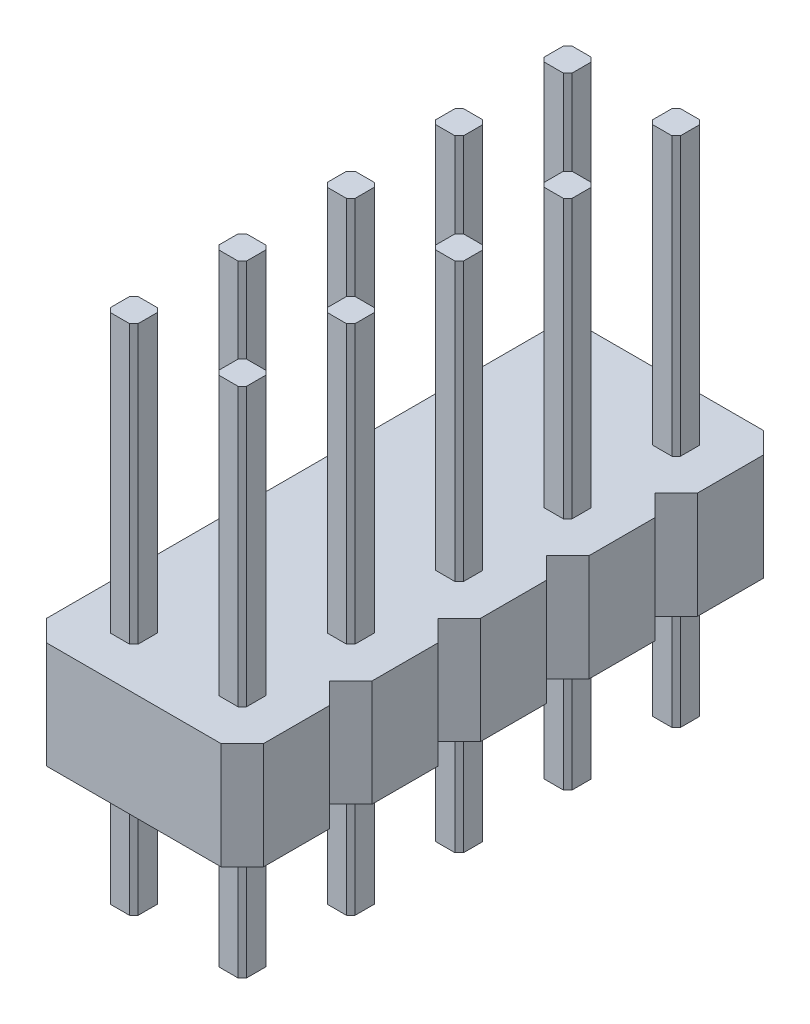
SolidWorks part; units mm, degrees
ref_plane "Front Plane" through (0, 0, 0) normal (0, 0, 1) x (1, 0, 0)
ref_plane "Top Plane" through (0, 0, 0) normal (0, 1, 0) x (1, 0, 0)
ref_plane "Right Plane" through (0, 0, 0) normal (1, 0, 0) x (0, 0, -1)
sketch "Sketch1" plane through (0, 0, 0) normal (0, 1, 0) x (1, 0, 0)
  line L0 (-0.325, 0.225) -> (-0.225, 0.325)
  line L1 (-0.225, 0.325) -> (0.225, 0.325)
  line L2 (-0.325, 0.225) -> (-0.325, -0.225)
  line L3 (-0.225, -0.325) -> (0.225, -0.325)
  line L4 (0.325, 0.225) -> (0.325, -0.225)
  line L5 (-0.325, 0.325) -> (0.325, -0.325) construction
  line L6 (-0.325, -0.325) -> (0.325, 0.325) construction
  line L7 (0.225, 0.325) -> (0.325, 0.225)
  line L8 (0.225, -0.325) -> (0.325, -0.225)
  line L9 (-0.325, -0.225) -> (-0.225, -0.325)
  point P0 (0, 0)
  dimension "D1" = 0.65
extrude "Boss-Extrude1" add sketch "Sketch1" along normal blind 12
pattern_linear "LPattern1" count 2 spacing 2.54 along (-1, 0, 0) of bodies 101
ref_plane "Plane1" through (0, 3, 0) normal (0, -1, 0) x (-1, 0, 0)
sketch "Sketch2" plane through (0, 3, 0) normal (0, -1, 0) x (-1, 0, 0)
  line L0 (-0.325, 0) -> (2.865, 0) construction
  line L1 (-0.325, -0.225) -> (-0.325, 0.225) construction
  line L2 (2.865, 0.225) -> (2.865, -0.225) construction
  line L3 (-1.27, 0.77) -> (-0.77, 1.27)
  line L4 (-0.77, 1.27) -> (3.31, 1.27)
  line L5 (-1.27, 0.77) -> (-1.27, -0.77)
  line L6 (-0.77, -1.27) -> (3.31, -1.27)
  line L7 (3.81, 0.77) -> (3.81, -0.77)
  line L8 (-1.27, 1.27) -> (3.81, -1.27) construction
  line L9 (-1.27, -1.27) -> (3.81, 1.27) construction
  line L10 (-1.27, -0.77) -> (-0.77, -1.27)
  line L11 (3.31, -1.27) -> (3.81, -0.77)
  line L12 (3.31, 1.27) -> (3.81, 0.77)
  point P6 (1.27, 0)
  dimension "D1" = 5.08
  dimension "D2" = 2.54
extrude "Boss-Extrude2" add sketch "Sketch2" against normal blind 2.5
pattern_linear "LPattern2" count 5 spacing 2.54 along (0, 0, -1) of bodies 103
combine bodies "Combine1" operation type add bodies to combine 103 104 105 106 107
